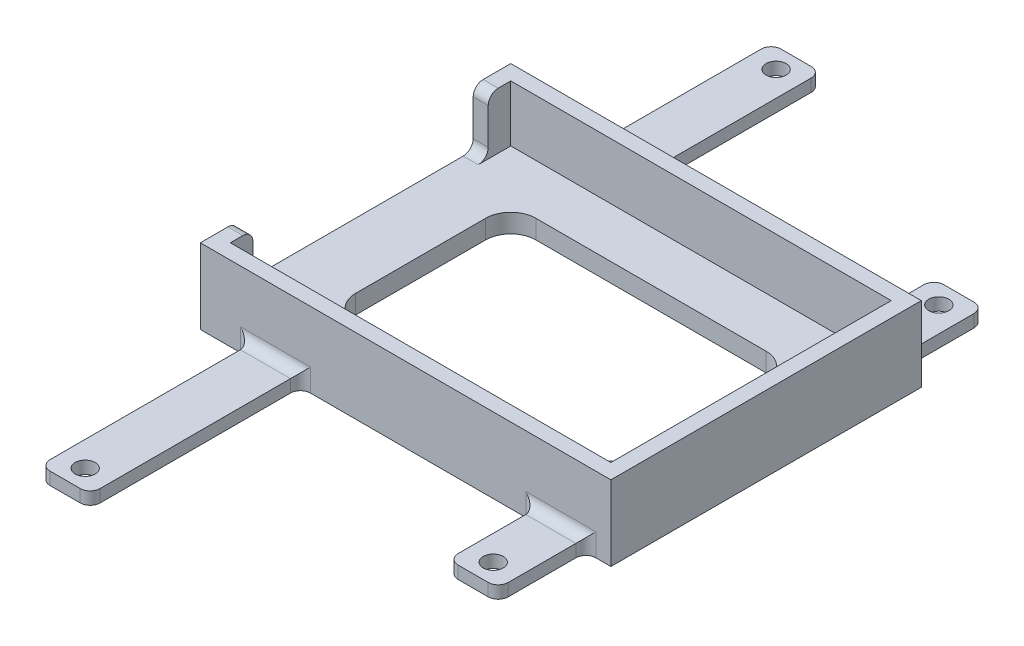
SolidWorks part; units mm, degrees
ref_plane "Front" through (0, 0, 0) normal (0, 0, 1) x (1, 0, 0)
ref_plane "Top" through (0, 0, 0) normal (0, 1, 0) x (1, 0, 0)
ref_plane "Right" through (0, 0, 0) normal (1, 0, 0) x (0, 0, -1)
sketch "Sketch1" plane through (0, 0, 0) normal (0, 1, 0) x (1, 0, 0)
  line L1 (0, 0) -> (104.14, 0)
  line L2 (0, 0) -> (0, 78.74)
  line L3 (0, 78.74) -> (104.14, 78.74)
  line L4 (104.14, 0) -> (104.14, 78.74)
  line L5 (0, 0) -> (104.14, 78.74) construction
  line L6 (0, 78.74) -> (104.14, 0) construction
  point P4 (52.07, 39.37)
  dimension "D1" = 78.74
  dimension "D2" = 104.14
extrude "Boss-Extrude1" add sketch "Sketch1" along normal blind 19.05
sketch "Sketch2" plane through (0, 19.05, 0) normal (0, 1, 0) x (1, 0, 0)
  line L0 (22.9045, 74.93) -> (22.9045, 78.74) construction
  line L1 (3.81, 3.81) -> (100.33, 3.81)
  line L2 (3.81, 3.81) -> (3.81, 74.93)
  line L3 (3.81, 74.93) -> (100.33, 74.93)
  line L4 (100.33, 3.81) -> (100.33, 74.93)
  line L5 (3.81, 3.81) -> (100.33, 74.93) construction
  line L6 (3.81, 74.93) -> (100.33, 3.81) construction
  line L7 (104.14, 78.74) -> (0, 78.74) construction
  line L8 (69.6553, 3.81) -> (69.6553, 0) construction
  line L9 (0, 0) -> (104.14, 0) construction
  line L10 (100.33, 20.843) -> (104.14, 20.843) construction
  line L11 (104.14, 0) -> (104.14, 78.74) construction
  line L12 (3.81, 57.6231) -> (0, 57.6231) construction
  line L13 (0, 78.74) -> (0, 0) construction
  point P4 (52.07, 39.37)
  dimension "D1" = 3.81
extrude "Cut-Extrude1" cut sketch "Sketch2" against normal offset from surface (14.2875 mm away) 4.7625 up to face at (52.07, 0, -39.37)
sketch "Sketch3" plane through (0, 4.7625, 0) normal (0, 1, 0) x (1, 0, 0)
  line L0 (76.502, 62.23) -> (76.502, 74.93) construction
  line L1 (22.86, 62.23) -> (81.28, 62.23)
  line L2 (16.51, 55.88) -> (16.51, 22.86)
  line L3 (22.86, 16.51) -> (81.28, 16.51)
  line L4 (87.63, 55.88) -> (87.63, 22.86)
  line L5 (16.51, 62.23) -> (87.63, 16.51) construction
  line L6 (16.51, 16.51) -> (87.63, 62.23) construction
  line L7 (100.33, 74.93) -> (3.81, 74.93) construction
  line L8 (87.63, 27.0645) -> (100.33, 27.0645) construction
  line L9 (100.33, 3.81) -> (100.33, 74.93) construction
  line L10 (33.0637, 16.51) -> (33.0637, 3.81) construction
  line L11 (3.81, 3.81) -> (100.33, 3.81) construction
  line L12 (16.51, 33.2472) -> (3.81, 33.2472) construction
  line L13 (3.81, 74.93) -> (3.81, 3.81) construction
  arc A0 (16.51, 22.86) -> (22.86, 16.51) centre (22.86, 22.86) ccw
  arc A1 (81.28, 16.51) -> (87.63, 22.86) centre (81.28, 22.86) ccw
  arc A2 (81.28, 62.23) -> (87.63, 55.88) centre (81.28, 55.88) cw
  arc A3 (22.86, 62.23) -> (16.51, 55.88) centre (22.86, 55.88) ccw
  point P4 (52.07, 39.37)
  dimension "D1" = 6.35
  dimension "D2" = 12.7
extrude "Cut-Extrude2" cut sketch "Sketch3" against normal up to next
sketch "Sketch4" plane through (0, 19.05, 0) normal (0, 1, 0) x (1, 0, 0)
  line L0 (3.81, 74.93) -> (3.81, 3.81) construction
  line L1 (3.81, 9.525) -> (0, 9.525)
  line L2 (3.81, 9.525) -> (3.81, 69.215)
  line L3 (3.81, 69.215) -> (0, 69.215)
  line L4 (0, 9.525) -> (0, 69.215)
  line L5 (3.81, 9.525) -> (0, 69.215) construction
  line L6 (3.81, 69.215) -> (0, 9.525) construction
  line L7 (0, 78.74) -> (0, 0) construction
  line L8 (1.905, 69.215) -> (1.905, 78.74) construction
  line L9 (104.14, 78.74) -> (0, 78.74) construction
  line L10 (1.905, 9.525) -> (1.905, 0) construction
  line L11 (0, 0) -> (104.14, 0) construction
  point P4 (1.905, 39.37)
  dimension "D1" = 9.525
extrude "Cut-Extrude3" cut sketch "Sketch4" against normal up to surface (14.2875 mm away) up to face at (52.07, 4.7625, -39.37)
fillet "Fillet1" radius 2.54 4 edges at (1.905, 19.05, -69.215) (1.905, 4.7625, -69.215) (1.905, 19.05, -9.525) (1.905, 4.7625, -9.525)
sketch "Sketch5" plane through (0, 0, 0) normal (0, -1, 0) x (1, 0, 0)
  line L0 (0, 0) -> (104.14, 0) construction
  line L1 (97.79, 0) -> (85.09, 0)
  line L2 (97.79, 0) -> (97.79, 19.685)
  line L3 (95.25, 22.225) -> (87.63, 22.225)
  line L4 (85.09, 0) -> (85.09, 19.685)
  line L5 (97.79, 0) -> (85.09, 22.225) construction
  line L6 (97.79, 22.225) -> (85.09, 0) construction
  line L7 (104.14, -39.37) -> (54.7699, -39.37) construction
  line L8 (104.14, 0) -> (104.14, -78.74) construction
  line L9 (97.79, -100.965) -> (85.09, -78.74) construction
  line L10 (97.79, -78.74) -> (85.09, -100.965) construction
  line L15 (85.09, -78.74) -> (85.09, -98.425)
  line L16 (95.25, -100.965) -> (87.63, -100.965)
  line L17 (97.79, -78.74) -> (97.79, -98.425)
  line L18 (97.79, -78.74) -> (85.09, -78.74)
  line L19 (0, -78.74) -> (0, 0) construction
  line L20 (12.7, 0) -> (25.4, 0)
  line L21 (12.7, 0) -> (12.7, 50.8)
  line L22 (15.24, 53.34) -> (22.86, 53.34)
  line L23 (25.4, 0) -> (25.4, 50.8)
  line L24 (12.7, 0) -> (25.4, 53.34) construction
  line L25 (12.7, 53.34) -> (25.4, 0) construction
  line L26 (12.7, -132.08) -> (25.4, -78.74) construction
  line L27 (12.7, -78.74) -> (25.4, -132.08) construction
  line L28 (25.4, -78.74) -> (25.4, -129.54)
  line L29 (15.24, -132.08) -> (22.86, -132.08)
  line L30 (12.7, -78.74) -> (12.7, -129.54)
  line L31 (12.7, -78.74) -> (25.4, -78.74)
  arc A0 (87.63, 22.225) -> (85.09, 19.685) centre (87.63, 19.685) ccw
  arc A1 (97.79, 19.685) -> (95.25, 22.225) centre (95.25, 19.685) ccw
  arc A6 (97.79, -98.425) -> (95.25, -100.965) centre (95.25, -98.425) cw
  arc A7 (87.63, -100.965) -> (85.09, -98.425) centre (87.63, -98.425) cw
  arc A8 (22.86, 53.34) -> (25.4, 50.8) centre (22.86, 50.8) cw
  arc A9 (12.7, 50.8) -> (15.24, 53.34) centre (15.24, 50.8) cw
  arc A10 (12.7, -129.54) -> (15.24, -132.08) centre (15.24, -129.54) ccw
  arc A11 (22.86, -132.08) -> (25.4, -129.54) centre (22.86, -129.54) ccw
  point P4 (91.44, 11.1125)
  point P27 (91.44, -89.8525)
  point P32 (19.05, 26.67)
  point P51 (19.05, -105.41)
  dimension "D3" = 2.54
  dimension "D4" = 6.35
  dimension "D7" = 2.54
  dimension "D1" = 22.225
  dimension "D2" = 12.7
  dimension "D5" = 12.7
  dimension "D6" = 12.7
  dimension "D8" = 50.8
extrude "Boss-Extrude2" add sketch "Sketch5" against normal blind 3.175
sketch "Sketch6" plane through (0, 3.175, 0) normal (0, 1, 0) x (1, 0, 0)
  line L0 (19.05, 132.08) -> (19.05, 127) construction
  line L1 (15.24, 132.08) -> (22.86, 132.08) construction
  line L2 (19.05, -48.26) -> (19.05, -53.34) construction
  line L4 (91.44, -22.225) -> (91.44, -17.145) construction
  line L5 (95.25, -22.225) -> (87.63, -22.225) construction
  line L6 (91.44, 100.965) -> (91.44, 95.885) construction
  line L7 (87.63, 100.965) -> (95.25, 100.965) construction
  line L8 (22.86, -53.34) -> (15.24, -53.34) construction
  circle A0 centre (19.05, 127) radius 2.54
  circle A1 centre (19.05, -48.26) radius 2.54
  circle A2 centre (91.44, -17.145) radius 2.54
  circle A3 centre (91.44, 95.885) radius 2.54
  dimension "D2" = 5.08
  dimension "D3" = 5.08
  dimension "D4" = 5.08
  dimension "D5" = 5.08
  dimension "D1" = 5.08
  dimension "D6" = 5.08
  dimension "D7" = 5.08
  dimension "D8" = 5.08
extrude "Cut-Extrude4" cut sketch "Sketch6" against normal up to next
fillet "Fillet2" radius 2.54 12 edges at (25.4, 1.5875, -78.74) (97.79, 1.5875, -78.74) (12.7, 1.5875, -78.74) (19.05, 3.175, -78.74) (85.09, 1.5875, -78.74) (91.44, 3.175, -78.74) (12.7, 1.5875, 0) (85.09, 1.5875, 0) (25.4, 1.5875, 0) (97.79, 1.5875, 0) (91.44, 3.175, 0) (19.05, 3.175, 0)
